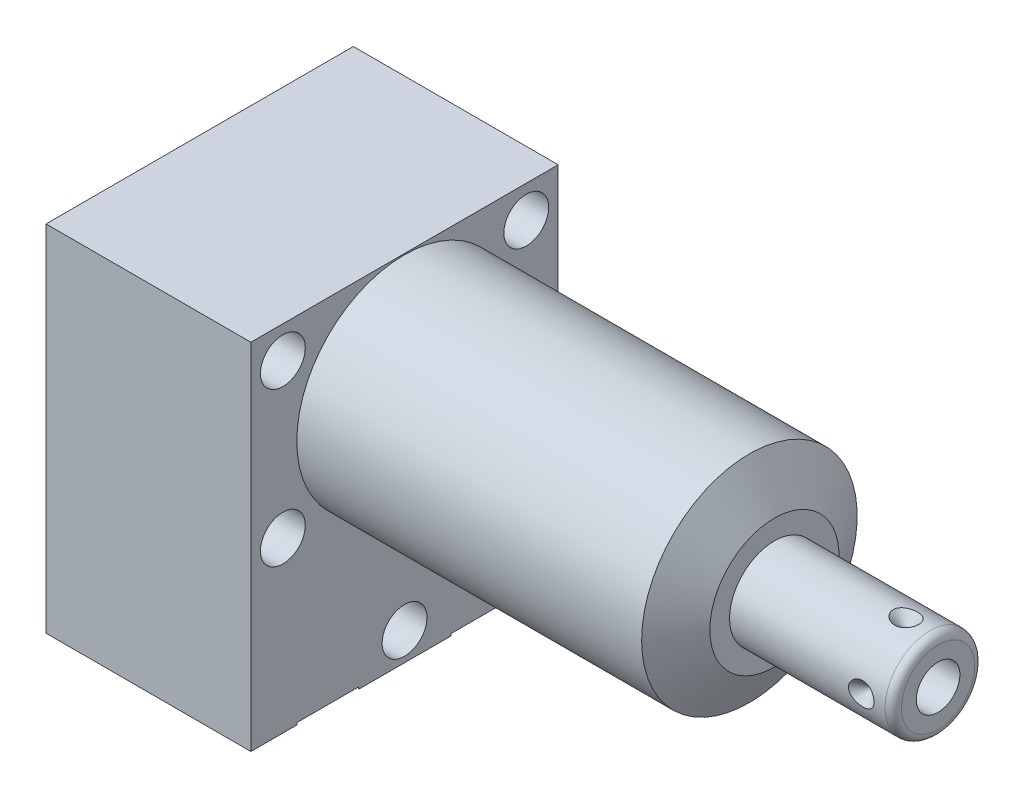
SolidWorks part; units mm, degrees
material "Alloy Steel"
ref_plane "Front Plane" through (0, 0, 0) normal (0, 0, 1) x (1, 0, 0)
ref_plane "Top Plane" through (0, 0, 0) normal (0, 1, 0) x (1, 0, 0)
ref_plane "Right Plane" through (0, 0, 0) normal (1, 0, 0) x (0, 0, -1)
ref_plane "Plane1" through (0, 0, 0) normal (1, 0, 0) x (0, 0, -1)
sketch "Sketch1" plane through (0, 0, 0) normal (1, 0, 0) x (0, 0, -1)
  line L0 (-19.05, 13.4874) -> (-19.05, -30.4546)
  line L1 (-19.05, -30.4546) -> (19.05, -30.4546)
  line L2 (19.05, -30.4546) -> (19.05, 13.4874)
  line L3 (19.05, 13.4874) -> (-19.05, 13.4874)
  line L4 (0, -32.6517) -> (0, 15.6845) construction
  dimension "D1" = 38.1
  dimension "D2" = 43.942
  dimension "D3" = 13.4874
extrude "Extrude1" add sketch "Sketch1" along normal blind 45.847 and the other way blind 25.4
ref_plane "Plane2" through (0, 0, 0) normal (1, 0, 0) x (0, 0, -1)
sketch "Sketch2" plane through (0, 0, 0) normal (1, 0, 0) x (0, 0, -1)
  line L0 (-14.6964, 0) -> (14.6964, 0) construction
  line L5 (19.05, 13.4874) -> (-19.05, 13.4874)
  line L6 (-19.05, 13.4874) -> (-19.05, -30.4546)
  line L7 (-19.05, -30.4546) -> (19.05, -30.4546)
  line L8 (19.05, -30.4546) -> (19.05, 13.4874)
  line L9 (19.05, 13.4874) -> (-19.05, 13.4874)
  line L10 (-19.05, 13.4874) -> (-19.05, -30.4546)
  line L11 (-19.05, -30.4546) -> (19.05, -30.4546)
  line L12 (19.05, -30.4546) -> (19.05, 13.4874)
  circle A0 centre (0, 0) radius 13.3604
  dimension "D1" = 26.7208
  dimension "D2" = 0
extrude "Cut-Extrude1" cut sketch "Sketch2" along normal up to next
ref_plane "Plane3" through (0, 0, 0) normal (0, 0, 1) x (1, 0, 0)
sketch "Sketch3" plane through (0, 0, 0) normal (0, 0, 1) x (1, 0, 0)
  line L0 (42.7527, 13.3604) -> (45.847, 8.001)
  line L1 (42.598, 0) -> (46.0017, 0) construction
  line L2 (45.847, 13.3604) -> (45.847, 8.001)
  line L3 (45.847, 13.3604) -> (42.7527, 13.3604)
  line L4 (45.847, 13.3604) -> (0, 13.3604) construction
  line L5 (45.847, -13.3604) -> (45.847, 13.3604) construction
  dimension "D1" = 30
  dimension "D2" = 16.002
revolve "Cut-Revolve1" cut sketch "Sketch3" angle 360 about L1
ref_plane "Plane4" through (-22.733, -19.8374, 9.525) normal (0, 0, 1) x (0, 1, 0)
sketch "S2D0002" plane through (-22.733, -19.8374, 9.525) normal (0, 0, 1) x (0, 1, 0)
  line L0 (-0.8128, 0) -> (3.7338, 0)
  line L1 (3.7338, 0) -> (3.2938, -2.0701)
  line L2 (3.2938, -2.0701) -> (2.6416, -2.7223)
  line L3 (2.6416, -2.7223) -> (2.6416, -13.97)
  line L4 (2.6416, -13.97) -> (-0.8128, -13.97)
  line L5 (-0.8128, -13.97) -> (-0.8128, 0)
  line L6 (-0.8128, -14.6685) -> (-0.8128, 0.6985) construction
  line L7 (19.8374, -65.4857) -> (19.8374, -22.733) construction
  dimension "D1" = 13.97
  dimension "D2" = 20.6502
revolve "Cut-Revolve2" cut sketch "S2D0002" angle 360 about L6
ref_plane "Plane5" through (-22.733, -19.8374, -9.525) normal (0, 0, 1) x (0, 1, 0)
sketch "Sketch5" plane through (-22.733, -19.8374, -9.525) normal (0, 0, 1) x (0, 1, 0)
  line L0 (-0.8128, 0) -> (3.7338, 0)
  line L1 (3.7338, 0) -> (3.2938, -2.0701)
  line L2 (3.2938, -2.0701) -> (2.6416, -2.7223)
  line L3 (2.6416, -2.7223) -> (2.6416, -13.97)
  line L4 (2.6416, -13.97) -> (-0.8128, -13.97)
  line L5 (-0.8128, -13.97) -> (-0.8128, 0)
  line L6 (-0.8128, -14.6685) -> (-0.8128, 0.6985) construction
  line L7 (19.8374, -65.4857) -> (19.8374, -22.733) construction
  dimension "D1" = 13.97
  dimension "D2" = 20.6502
revolve "Cut-Revolve3" cut sketch "Sketch5" angle 360 about L6
ref_plane "Plane6" through (-8.7376, -30.2006, 9.525) normal (0, 0, 1) x (-1, 0, 0)
sketch "Sketch14" plane through (-25.4, 0, 0) normal (-1, 0, 0) x (0, 0, 1)
  circle A0 centre (-9.525, -20.6502) radius 7.9375
  circle A1 centre (9.525, -20.6502) radius 7.9375
  dimension "D1" = 15.875
extrude "Cut-Extrude2" cut sketch "Sketch14" against normal blind 2.667
sketch "Sketch6" plane through (-8.7376, -30.2006, 9.525) normal (0, 0, 1) x (-1, 0, 0)
  line L0 (16.6624, -43.688) -> (16.6624, 0.254) construction
  line L1 (6.1836, 0) -> (5.641, -2.5527)
  line L2 (5.641, -2.5527) -> (4.9771, -3.2166)
  line L3 (4.9771, -3.2166) -> (4.9771, -17.272)
  line L4 (4.9771, -17.272) -> (0, -17.272)
  line L5 (0, -17.272) -> (0, 0)
  line L6 (0, -18.1356) -> (0, 0.8636) construction
  line L7 (6.1836, 0) -> (9.5237, 0)
  line L8 (9.5237, 0) -> (9.5237, 0.254)
  line L9 (16.6624, 0.254) -> (-8.7376, 0.254) construction
  line L10 (9.5237, 0.254) -> (0, 0.254)
  line L11 (0, 0.254) -> (0, 0)
  dimension "D1" = 19.0475
  dimension "D2" = 0.254
  dimension "D3" = 16.6624
revolve "Cut-Revolve4" cut sketch "Sketch6" angle 360 about L6
ref_plane "Plane7" through (-8.7376, -30.2006, -9.525) normal (0, 0, 1) x (-1, 0, 0)
sketch "Sketch7" plane through (-8.7376, -30.2006, -9.525) normal (0, 0, 1) x (-1, 0, 0)
  line L0 (16.6624, -43.688) -> (16.6624, 0.254) construction
  line L1 (6.1849, 0) -> (5.6423, -2.5527)
  line L2 (5.6423, -2.5527) -> (4.9784, -3.2166)
  line L3 (4.9784, -3.2166) -> (4.9784, -17.272)
  line L4 (4.9784, -17.272) -> (0, -17.272)
  line L5 (0, -17.272) -> (0, 0)
  line L6 (0, -18.1356) -> (0, 0.8636) construction
  line L7 (6.1849, 0) -> (9.5237, 0)
  line L8 (9.5237, 0) -> (-8.7376, 0) construction
  line L9 (9.5237, 0) -> (9.5237, 0.254)
  line L10 (16.6624, 0.254) -> (-8.7376, 0.254) construction
  line L11 (9.5237, 0.254) -> (0, 0.254)
  line L12 (0, 0.254) -> (0, 0)
  dimension "D1" = 16.6624
  dimension "D2" = 9.9568
  dimension "D3" = 19.0475
revolve "Cut-Revolve5" cut sketch "Sketch7" angle 360 about L6
ref_plane "Plane8" through (0, 0, 0) normal (0, 0, 1) x (1, 0, 0)
sketch "Sketch8" plane through (0, 0, 0) normal (0, 0, 1) x (1, 0, 0)
  line L0 (45.847, 0) -> (45.847, 5.5562)
  line L1 (45.847, 5.5562) -> (65.1256, 5.5562)
  line L2 (66.1416, 4.5403) -> (66.1416, 0)
  line L3 (66.1416, 0) -> (45.847, 0)
  line L4 (44.8323, 0) -> (67.1563, 0) construction
  line L5 (45.847, -8.001) -> (45.847, 8.001) construction
  line L6 (-25.4, 13.4874) -> (-25.4, -30.4546) construction
  arc A0 (66.1416, 4.5403) -> (65.1256, 5.5562) centre (65.1256, 4.5403) ccw
  point P0 (45.847, 0)
  dimension "D3" = 1.016
  dimension "D1" = 91.5416
  dimension "D2" = 11.1125
revolve "Revolve1" add sketch "Sketch8" angle 360 about L4
ref_plane "Plane9" through (66.1416, -2.8067, 0) normal (0, 0, 1) x (0, -1, 0)
sketch "S2D0001" plane through (66.1416, -2.8067, 0) normal (0, 0, 1) x (0, -1, 0)
  line L0 (-0.1016, 0) -> (-0.1016, -9.652)
  line L1 (-0.1016, -9.652) -> (-2.8067, -11.2774)
  line L2 (-0.1016, 0) -> (-2.8067, 0)
  line L3 (-2.8067, 0) -> (-2.8067, -11.2774)
  line L4 (-2.8067, -12.4388) -> (-2.8067, 0.5923) construction
  line L5 (1.7335, 0) -> (-7.3469, 0) construction
  dimension "D1" = 5.4102
  dimension "D2" = 9.652
  dimension "D3" = 59
revolve "Cut-Revolve6" cut sketch "S2D0001" angle 360 about L4
ref_plane "Plane10" through (-25.4, -30.2006, 0) normal (0, -1, 0) x (0, 0, -1)
sketch "Sketch10" plane through (-25.4, -30.2006, 0) normal (0, -1, 0) x (0, 0, -1)
  circle A0 centre (-9.525, 16.6624) radius 6.4389
  circle A1 centre (-9.525, 16.6624) radius 6.1836 construction
  dimension "D1" = 12.8778
extrude "Extrude2" add sketch "Sketch10" along normal blind 1.651
sketch "Sketch11" plane through (-22.733, 0, 0) normal (-1, 0, 0) x (0, 0, 1)
  circle A0 centre (9.525, -20.6502) radius 4.8006
  circle A1 centre (9.525, -20.6502) radius 4.5466 construction
  dimension "D1" = 9.6012
ref_plane "Plane11" through (-25.4, 0, 0) normal (1, 0, 0) x (0, 0, -1)
extrude "Extrude3" add sketch "Sketch11" along normal up to surface (2.667 mm away) up to plane "Plane11"
ref_plane "Plane12" through (62.1792, -5.5562, 0) normal (0, 0, 1) x (-1, 0, 0)
ref_plane "Plane13" through (0, 0, 0) normal (0, 0, 1) x (-1, 0, 0)
sketch "Sketch12" plane through (62.1792, 5.5563, 0) normal (0, 0, -1) x (-1, 0, 0)
  line L0 (0, 0) -> (1.5875, 0)
  line L1 (1.5875, 0) -> (0, -1.5875)
  line L2 (0, 0) -> (0, -1.5875)
  line L3 (0, -3.434) -> (0, 0.0794) construction
  line L4 (16.3322, 0) -> (-2.9464, 0) construction
  line L5 (-3.9624, -1.016) -> (-3.9624, -10.0965) construction
  dimension "D1" = 3.9624
  dimension "D2" = 45
  dimension "D3" = 3.175
revolve "Cut-Revolve7" cut sketch "Sketch12" angle 360 about L3
pattern_circular "CirPattern1" count 4 over 360 about axis through (45.848, 0, 0) along (-1, 0, 0) of "Cut-Revolve7"
hole_wizard "Hole1" positions "Sketch17" profile "Sketch16" legacy end condition up to next
sketch "Sketch17" plane through (0, 0, 0) normal (1, 0, 0) x (0, 0, -1)
  line L0 (0, 0) -> (0, 17.9298) construction
  line L1 (0, 0) -> (-24.6425, 0) construction
  point P0 (-15.0876, 9.525)
  point P10 (-15.0876, -9.525)
  point P12 (15.0876, 9.525)
  point P13 (15.0876, -9.525)
  point P14 (0, -26.9748)
  dimension "D1" = 9.525
  dimension "D2" = 15.0876
  dimension "D3" = 26.9748
sketch "Sketch16" plane through (0, 9.525, 15.0876) normal (0, 1, 0) x (0, 0, -1)
  line L0 (0, 0) -> (0, 25.4)
  line L1 (0, 25.4) -> (2.7813, 25.4)
  line L2 (2.7813, 25.4) -> (2.7813, 0)
  line L3 (2.7813, 0) -> (0, 0)
  line L4 (0, 110) -> (0, -10) construction
  dimension "Diameter" = 5.5626
  dimension "Depth" = 25.4
